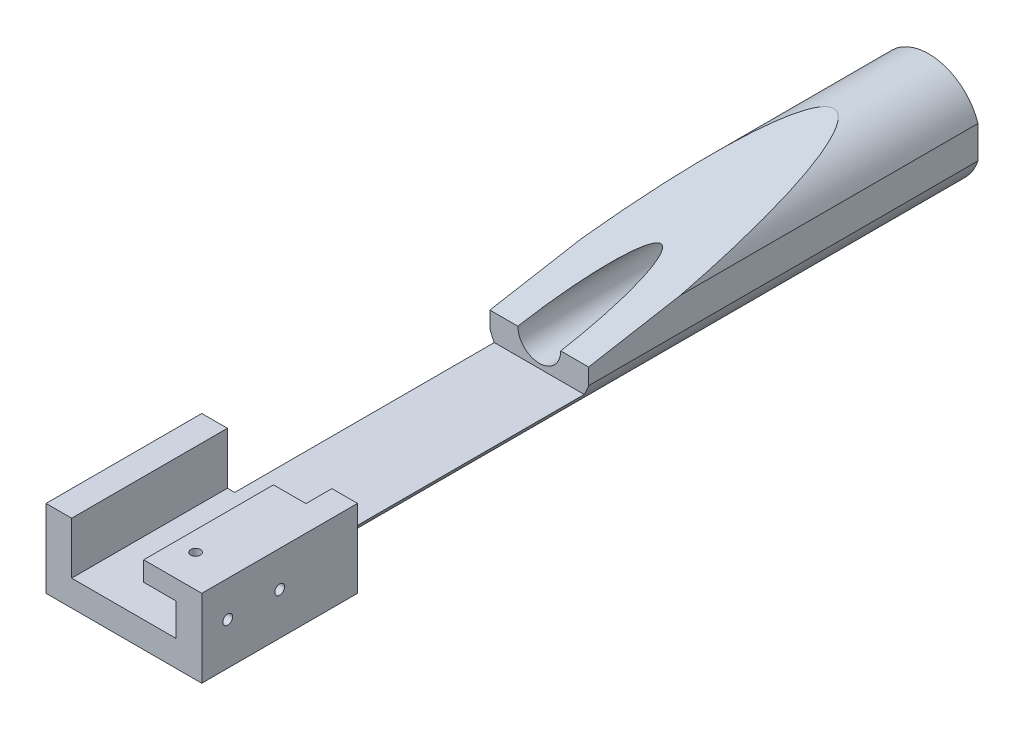
SolidWorks part; units mm, degrees
material "Copper"
ref_plane "Ebene vorne" through (0, 0, 0) normal (0, 0, 1) x (1, 0, 0)
ref_plane "Ebene oben" through (0, 0, 0) normal (0, 1, 0) x (1, 0, 0)
ref_plane "Ebene rechts" through (0, 0, 0) normal (1, 0, 0) x (0, 0, -1)
sketch "Sketch1" plane through (0, 0, 0) normal (0, 0, 1) x (1, 0, 0)
  circle A0 centre (0, 0) radius 4
extrude "Boss-Extrude1" add sketch "Sketch1" along normal blind 50
sketch "Sketch2" plane through (0, 0, 50) normal (0, 0, 1) x (1, 0, 0)
  line L1 (-6, 2) -> (6, 2)
  line L2 (-6, 2) -> (-6, -4)
  line L3 (-6, -4) -> (6, -4)
  line L4 (6, 2) -> (6, -4)
  circle A0 centre (0, 0) radius 4 construction
  point P7 (0, -4)
  dimension "D1" = 6
  dimension "D2" = 12
extrude "Boss-Extrude2" add sketch "Sketch2" along direction (0, 0, 1) on the side of the normal blind 12
sketch "Sketch3" plane through (0, 2, 0) normal (0, 1, 0) x (1, 0, 0)
  line L1 (-4.025, -30) -> (4.025, -30)
  line L2 (-4.025, -30) -> (-4.025, -62)
  line L3 (-4.025, -62) -> (4.025, -62)
  line L4 (4.025, -30) -> (4.025, -62)
  line L5 (6, -62) -> (-6, -62) construction
  point P12 (0, -62)
  dimension "D1" = 8.05
extrude "Cut-Extrude1" cut sketch "Sketch3" against normal blind 4
sketch "Sketch4" plane through (0, 0, 30) normal (0, 0, 1) x (1, 0, 0)
  line L1 (-10, 0) -> (10, 0)
  arc A0 (-10, 0) -> (10, 0) centre (0, 0) cw
extrude "Cut-Extrude3" cut sketch "Sketch4" against normal blind 30 draft 10
sketch "Sketch6" plane through (0, -2, 0) normal (0, 1, 0) x (1, 0, 0)
  line L0 (-1.4497, -62) -> (0, -58.5)
  line L1 (0, -58.5) -> (1.4497, -62)
  line L2 (1.4497, -62) -> (-1.4497, -62)
  line L4 (-4.025, -62) -> (4.025, -62) construction
  line L5 (3.4641, -41.3426) -> (-3.4641, -41.3426) construction
  point P14 (0, -41.3426)
  dimension "D1" = 45
  dimension "D2" = 3.5
hole_wizard "Tap Drill for M4x0.7 Tap1" positions "Sketch24" profile "Sketch25" hole size "M4x0.7" standard "ANSI Metric" end condition up to next
sketch "Sketch24" plane through (0, 0, 0) normal (0, 0, -1) x (-1, 0, 0)
  point P0 (0, 0)
sketch "Sketch25" plane through (0, 0, 0) normal (1, 0, 0) x (0, 1, 0)
  line L0 (0, 0) -> (0, 30.001)
  line L1 (0, 30.001) -> (1.65, 30.001)
  line L2 (1.65, 30.001) -> (1.65, 0)
  line L5 (1.65, 0) -> (0, 0)
  line L11 (0, -6.35) -> (0, 107.95) construction
  dimension "Thru Hole Dia." = 3.3
  dimension "Thru Hole Depth" = 30.001
sketch "Sketch26" plane through (0, 0, 0) normal (0, 0, -1) x (-1, 0, 0)
  line L0 (-6, 2) -> (-4.025, 2) construction
  line L1 (-4.025, 2) -> (-3.8, 2)
  line L2 (-4.025, 2) -> (-4.025, -4)
  line L3 (-4.025, -4) -> (-3.8, -4)
  line L4 (-3.8, 2) -> (-3.8, -4)
  line L5 (0, -4) -> (-6, -4) construction
  line L6 (-4.025, -2) -> (-4.025, 2) construction
  line L7 (4.025, 2) -> (3.8, 2)
  line L8 (4.025, 2) -> (4.025, -4)
  line L9 (4.025, -4) -> (3.8, -4)
  line L10 (3.8, 2) -> (3.8, -4)
  line L11 (4.025, 2) -> (4.025, -2) construction
  line L12 (4.025, 2) -> (6, 2) construction
  line L13 (6, -4) -> (0, -4) construction
extrude "Cut-Extrude4" cut sketch "Sketch26" against normal blind 50
sketch "Sketch28" plane through (0, 0, 50) normal (0, 0, 1) x (1, 0, 0)
  line L1 (-3.4641, 2) -> (3.4641, 2)
  line L2 (-3.4641, 2) -> (3.4641, 2)
  arc A1 (3.4641, 2) -> (-3.4641, 2) centre (0, 0) ccw
  arc A2 (3.4641, 2) -> (-3.4641, 2) centre (0, 0) ccw
  dimension "D1" = 0
extrude "Cut-Extrude5" cut sketch "Sketch28" against normal up to next (20 mm away)
hole_wizard "Tap Drill for M1x0.25 Tap1" positions "Sketch29" profile "Sketch30" hole size "M1x0.25" standard "JIS"
sketch "Sketch29" plane through (4.025, 0, 0) normal (-1, 0, 0) x (0, 0, 1)
  line L0 (62, -2) -> (50, -2) construction
  line L1 (62, -2) -> (62, 2) construction
  point P0 (60, -0.75)
  point P8 (56, -0.75)
  dimension "D1" = 1.25
  dimension "D2" = 2
  dimension "D3" = 1.25
  dimension "D4" = 4
sketch "Sketch30" plane through (4.025, -0.75, 60) normal (0, 1, 0) x (0, 0, 1)
  line L0 (0, 0) -> (0, 1.975)
  line L1 (0, 1.975) -> (0.375, 1.975)
  line L2 (0.375, 1.975) -> (0.375, 0)
  line L5 (0.375, 0) -> (0, 0)
  line L11 (0, -6.35) -> (0, 107.95) construction
  dimension "Thru Hole Dia." = 0.75
  dimension "Thru Hole Depth" = 1.975
sketch "Sketch31" plane through (0, 0, 62) normal (0, 0, 1) x (1, 0, 0)
  line L1 (1.525, 2) -> (6, 2)
  line L2 (1.525, 2) -> (1.525, 0.5)
  line L3 (1.525, 0.5) -> (6, 0.5)
  line L4 (6, 2) -> (6, 0.5)
  line L5 (1.525, 2) -> (6, 0.5) construction
  line L6 (1.525, 0.5) -> (6, 2) construction
  line L8 (-4.025, -2) -> (-4.025, 2)
  line L9 (-4.025, 2) -> (-6, 2)
  line L10 (-6, 2) -> (-6, -4)
  line L11 (-6, -4) -> (6, -4)
  line L12 (6, -4) -> (6, 2)
  line L13 (6, 2) -> (4.025, 2)
  line L14 (4.025, 2) -> (4.025, -2)
  line L15 (4.025, -2) -> (-4.025, -2)
  line L16 (-4.025, -2) -> (-4.025, 2)
  line L17 (-4.025, 2) -> (-6, 2)
  line L18 (-6, 2) -> (-6, -4)
  line L19 (-6, -4) -> (6, -4)
  line L20 (6, -4) -> (6, 2)
  line L21 (6, 2) -> (4.025, 2)
  line L22 (4.025, 2) -> (4.025, -2)
  line L23 (4.025, -2) -> (-4.025, -2)
  point P2 (3.7625, 1.25)
  line M19 (4.025, 2) -> (4.025, -2)
  dimension "D2" = 2.5
  dimension "D3" = 0
  dimension "D4" = 2.5
  dimension "D5" = 0
  dimension "D1" = 0
extrude "Boss-Extrude3" add sketch "Sketch31" against normal blind 10 contours L2 L3 L1 M19
ref_plane "Plane1" through (3.4641, -2, 30) normal (-1, 0, 0) x (0, 0, 1)
hole_wizard "Tap Drill for M1x0.25 Tap2" positions "Sketch33" profile "Sketch34" hole size "M1x0.25" standard "JIS"
sketch "Sketch33" plane through (0, 2, 0) normal (0, 1, 0) x (1, 0, 0)
  line L0 (1.525, -52) -> (1.525, -62) construction
  line L1 (6, -62) -> (1.525, -62) construction
  point P0 (3.025, -59.5)
  dimension "D1" = 1.5
  dimension "D2" = 2.5
sketch "Sketch34" plane through (3.025, 2, 59.5) normal (1, 0, 0) x (0, 0, 1)
  line L0 (0, 0) -> (0, 1.5)
  line L1 (0, 1.5) -> (0.375, 1.5)
  line L2 (0.375, 1.5) -> (0.375, 0)
  line L5 (0.375, 0) -> (0, 0)
  line L11 (0, -6.35) -> (0, 107.95) construction
  dimension "Thru Hole Dia." = 0.75
  dimension "Thru Hole Depth" = 1.5
ref_plane "Plane2" through (-3.4641, -2, 30) normal (-1, 0, 0) x (0, 0, 1)
